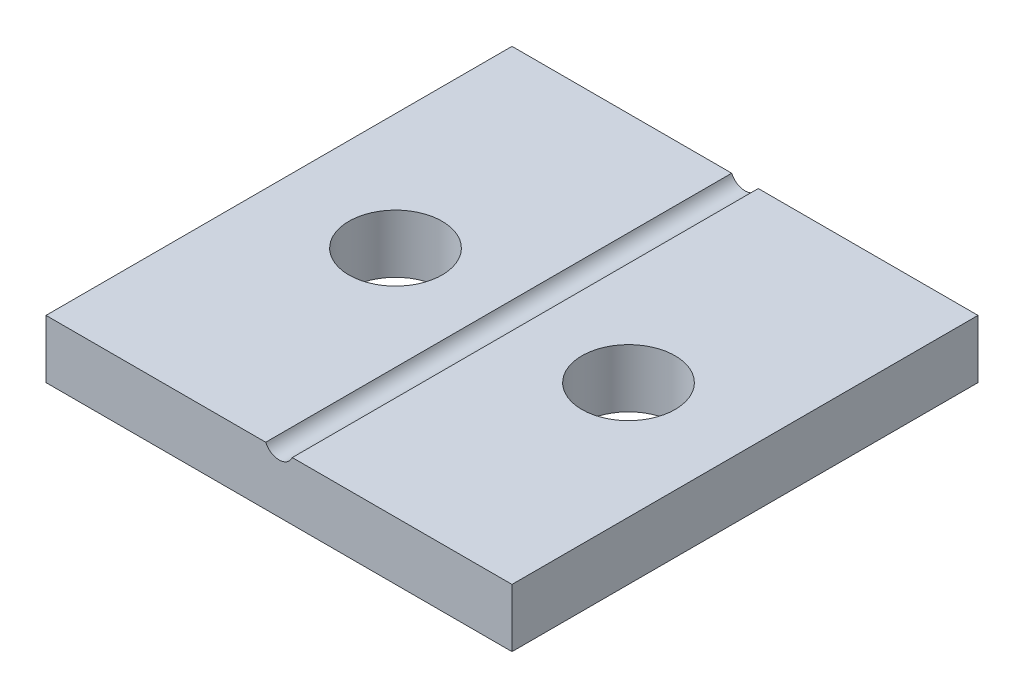
SolidWorks part; units mm, degrees
ref_plane "Front Plane" through (0, 0, 0) normal (0, 0, 1) x (1, 0, 0)
ref_plane "Top Plane" through (0, 0, 0) normal (0, 1, 0) x (1, 0, 0)
ref_plane "Right Plane" through (0, 0, 0) normal (1, 0, 0) x (0, 0, -1)
sketch "Sketch1" plane through (0, 0, 0) normal (0, 1, 0) x (1, 0, 0)
  line L1 (-60.7547, 52.0755) -> (-40.7547, 52.0755)
  line L2 (-60.7547, 52.0755) -> (-60.7547, 32.0755)
  line L3 (-60.7547, 32.0755) -> (-40.7547, 32.0755)
  line L4 (-40.7547, 52.0755) -> (-40.7547, 32.0755)
  dimension "D1" = 20
  dimension "D2" = 20
extrude "Boss-Extrude1" add sketch "Sketch1" along normal blind 2.5
sketch "Sketch2" plane through (0, 0, -32.0755) normal (0, 0, 1) x (1, 0, 0)
  line L0 (-60.7547, 2.5) -> (-40.7547, 2.5) construction
  line L1 (-50.7547, 6.7696) -> (-50.7547, 3.4135) construction
  circle A0 centre (-50.7547, 2.75) radius 0.6223
  point P6 (-50.7547, 2.5)
  dimension "D2" = 1.2446
  dimension "D1" = 0.25
extrude "Cut-Extrude1" cut sketch "Sketch2" against normal through all contours A0
sketch "Sketch3" plane through (0, 2.5, 0) normal (0, 1, 0) x (1, 0, 0)
  line L0 (-55.7547, 42.0755) -> (-45.7547, 42.0755) construction
  line L3 (-60.7547, 52.0755) -> (-40.7547, 32.0755) construction
  line L4 (-40.7547, 52.0755) -> (-60.7547, 32.0755) construction
  circle A0 centre (-55.7547, 42.0755) radius 2
  circle A1 centre (-45.7547, 42.0755) radius 2
  point P2 (-50.7547, 42.0755)
  dimension "D2" = 4
  dimension "D1" = 10
extrude "Cut-Extrude2" cut sketch "Sketch3" against normal through all
